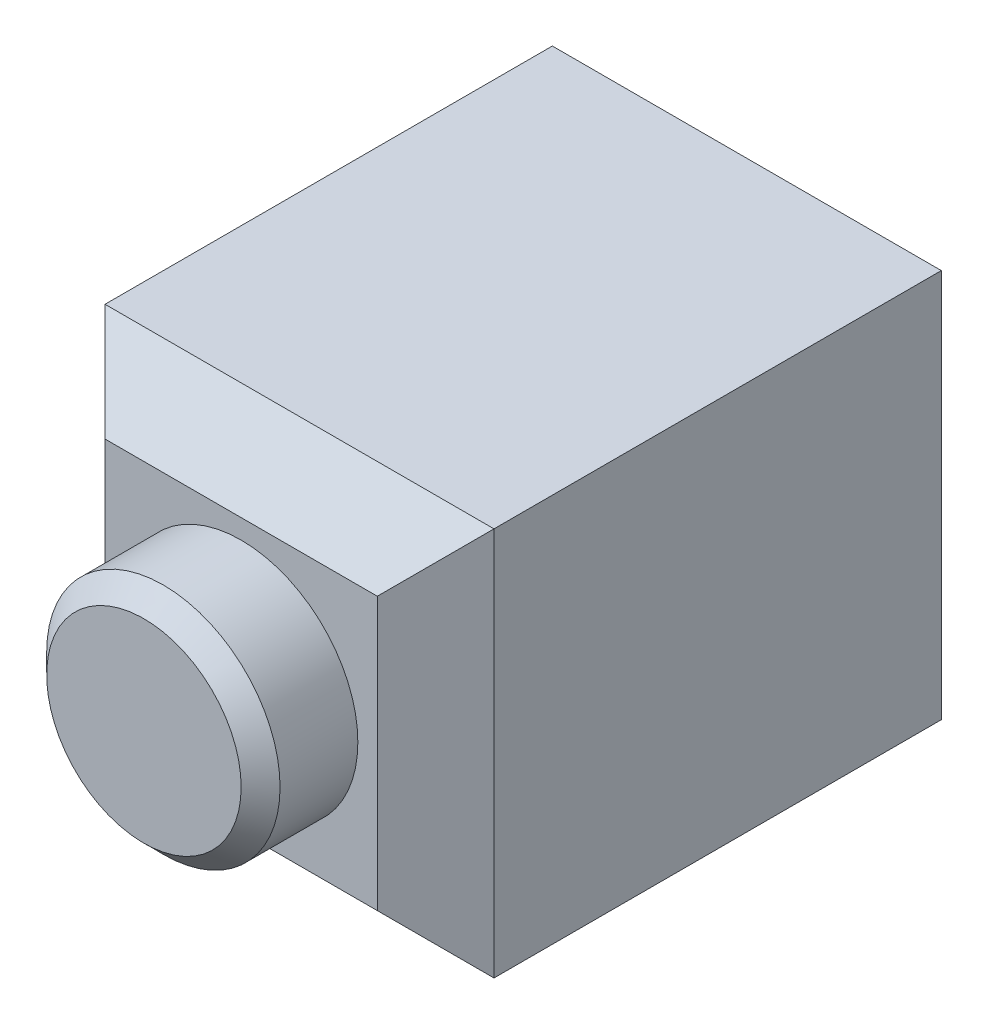
SolidWorks part; units mm, degrees
ref_plane "Front Plane" through (0, 0, 0) normal (0, 0, 1) x (1, 0, 0)
ref_plane "Top Plane" through (0, 0, 0) normal (0, 1, 0) x (1, 0, 0)
ref_plane "Right Plane" through (0, 0, 0) normal (1, 0, 0) x (0, 0, -1)
sketch "Sketch1" plane through (0, 0, 0) normal (0, 0, 1) x (1, 0, 0)
  line L1 (-17.7099, 6.5911) -> (2.2901, 6.5911)
  line L2 (-17.7099, 6.5911) -> (-17.7099, -13.4089)
  line L3 (-17.7099, -13.4089) -> (2.2901, -13.4089)
  line L4 (2.2901, 6.5911) -> (2.2901, -13.4089)
  dimension "D1" = 20
  dimension "D2" = 20
extrude "Extrude1" add sketch "Sketch1" along normal blind 26
chamfer "Chamfer1" distance 3 angle 45 4 edges at (-7.7099, 6.5911, 26) (2.2901, -3.4089, 26) (-7.7099, -13.4089, 26) (-17.7099, -3.4089, 26)
sketch "Sketch3" plane through (0, 0, 26) normal (0, 0, 1) x (1, 0, 0)
  line L0 (-14.7099, 3.5911) -> (-0.7099, -10.4089) construction
  circle A0 centre (-7.7099, -3.4089) radius 6
  point P6 (-7.7099, -3.4089)
  dimension "D1" = 12
extrude "Extrude3" add sketch "Sketch3" along normal blind 5
chamfer "Chamfer2" distance 1 angle 45 1 edges at (-1.7099, -3.4089, 31)
